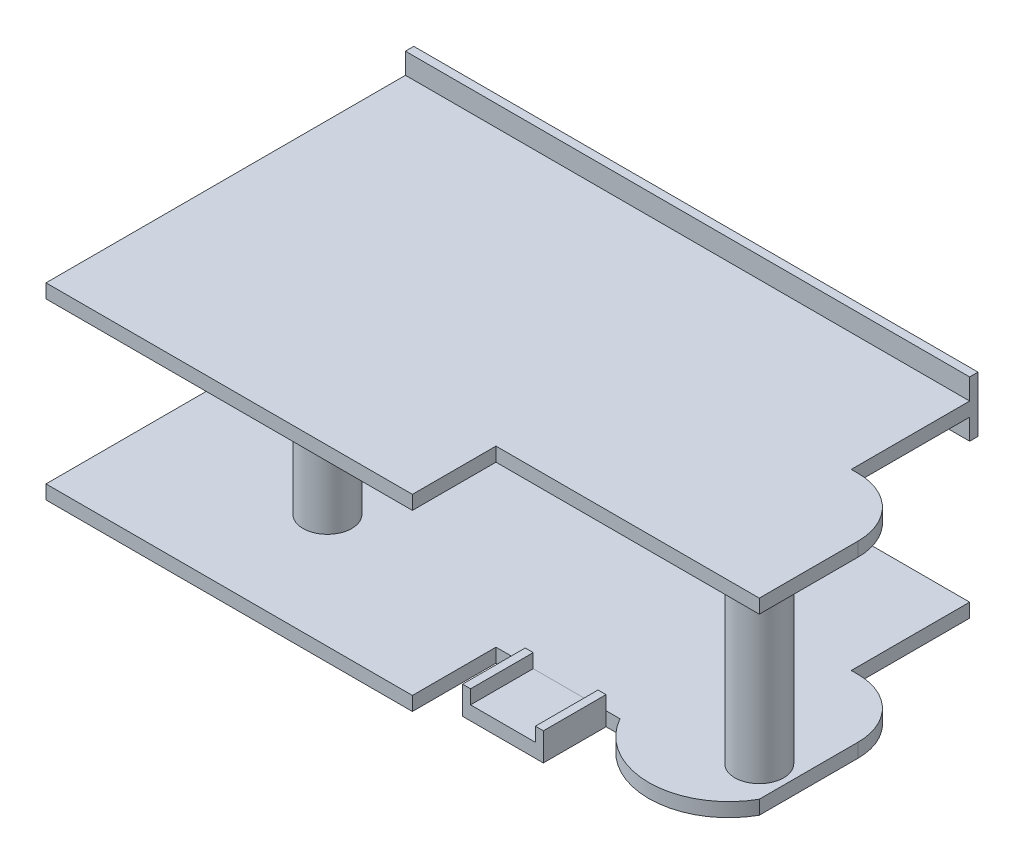
SolidWorks part; units mm, degrees
ref_plane "Vorne" through (0, 0, 0) normal (0, 0, 1) x (1, 0, 0)
ref_plane "Oben" through (0, 0, 0) normal (0, 1, 0) x (1, 0, 0)
ref_plane "Rechts" through (0, 0, 0) normal (1, 0, 0) x (0, 0, -1)
sketch "Skizze0" plane through (0, 0, 0) normal (0, 1, 0) x (1, 0, 0)
  line L0 (0, 0) -> (263, 0)
  line L1 (263, 0) -> (263, 60)
  line L2 (452, 60) -> (452, 173)
  line L3 (0, 258) -> (405, 258)
  line L4 (0, 0) -> (0, 258)
  line L5 (263, 60) -> (452, 60)
  line L6 (405, 258) -> (405, 173)
  line L7 (405, 173) -> (452, 173)
  dimension "D1" = 452
  dimension "D2" = 258
  dimension "D3" = 263
  dimension "D4" = 198
  dimension "D5" = 405
  dimension "D6" = 85
extrude "Aufsatz-Linear austragen0" add sketch "Skizze0" against normal blind 10
sketch "Skizze1" plane through (0, 0, 0) normal (0, 1, 0) x (1, 0, 0)
  line L0 (0, 258) -> (0, 0) construction
  line L1 (263, 60) -> (452, 60) construction
  line L2 (452, 60) -> (452, 173) construction
  circle A0 centre (120, 82) radius 17.5
  circle A1 centre (430, 82) radius 17.5
  dimension "D1" = 35
  dimension "D2" = 120
  dimension "D3" = 22
  dimension "D4" = 22
extrude "Aufsatz-Linear austragen1" add sketch "Skizze1" along normal blind 115
sketch "Skizze2" plane through (0, 115, 115) normal (0, 1, 0) x (1, 0, 0)
  line L0 (0, 115) -> (263, 115)
  line L1 (263, 115) -> (263, 175)
  line L2 (452, 175) -> (452, 288)
  line L3 (0, 373) -> (405, 373)
  line L4 (0, 115) -> (0, 373)
  line L5 (263, 175) -> (452, 175)
  line L6 (405, 373) -> (405, 288)
  line L7 (405, 288) -> (452, 288)
  dimension "D1" = 452
  dimension "D2" = 258
  dimension "D3" = 263
  dimension "D4" = 198
  dimension "D5" = 405
  dimension "D6" = 85
extrude "Aufsatz-Linear austragen2" add sketch "Skizze2" along normal blind 10
fillet "Verrundung1" radius 42 2 edges at (452, -5, -173) (452, 120, -173)
sketch "Skizze3" plane through (0, 0, 0) normal (0, 1, 0) x (1, 0, 0)
  line L0 (452, 60) -> (352, 60)
  line L1 (263, 60) -> (452, 60) construction
  arc A0 (352, 60) -> (452, 60) centre (402, 88) ccw
  dimension "D2" = 28
  dimension "D1" = 100
extrude "Aufsatz-Linear austragen3" add sketch "Skizze3" against normal up to surface (10 mm away) up to face at (295.4109, -10, -124.6332)
sketch "Skizze4" plane through (0, 0, -258) normal (0, 0, -1) x (-1, 0, 0)
  line L0 (-405, 125) -> (0, 125) construction
  line L1 (-405, 100) -> (0, 100)
  line L2 (-405, 100) -> (-405, 140)
  line L3 (-405, 140) -> (0, 140)
  line L4 (0, 100) -> (0, 140)
  dimension "D1" = 40
  dimension "D2" = 15
extrude "Aufsatz-Linear austragen4" add sketch "Skizze4" along normal blind 6
sketch "Bahn" plane through (0, 0, 0) normal (0, 1, 0) x (1, 0, 0)
  line L0 (263, 60) -> (452, 60) construction
  line L1 (405, 173) -> (405, 258) construction
  line L2 (468, 120) -> (468, 60)
  line L3 (342, 60) -> (342, 70)
  line L4 (405, 183) -> (395, 183)
  arc A0 (342, 60) -> (468, 60) centre (405, 60) ccw
  arc A1 (405, 183) -> (468, 120) centre (405, 120) cw
  dimension "D1" = 10
  dimension "D2" = 10
  dimension "D3" = 10
sketch "Profil" plane through (0, 0, -60) normal (0, 0, 1) x (1, 0, 0)
  line L0 (284, 10) -> (284, -10)
  line L1 (263, -10) -> (352, -10) construction
  line L2 (284, -10) -> (342, -10)
  line L3 (342, -10) -> (342, 10)
  line L4 (342, 10) -> (336.25, 10)
  line L5 (336.25, 10) -> (336.25, 0)
  line L6 (336.25, 0) -> (289.75, 0)
  line L7 (289.75, 0) -> (289.75, 10)
  line L8 (289.75, 10) -> (284, 10)
  line L9 (263, 0) -> (352, 0) construction
  dimension "D1" = 58
  dimension "D2" = 46.5
  dimension "D3" = 5.75
  dimension "D4" = 10
extrude "Hier soll 'ne Kurve draus werden" add sketch "Profil" along normal blind 45 separate body
